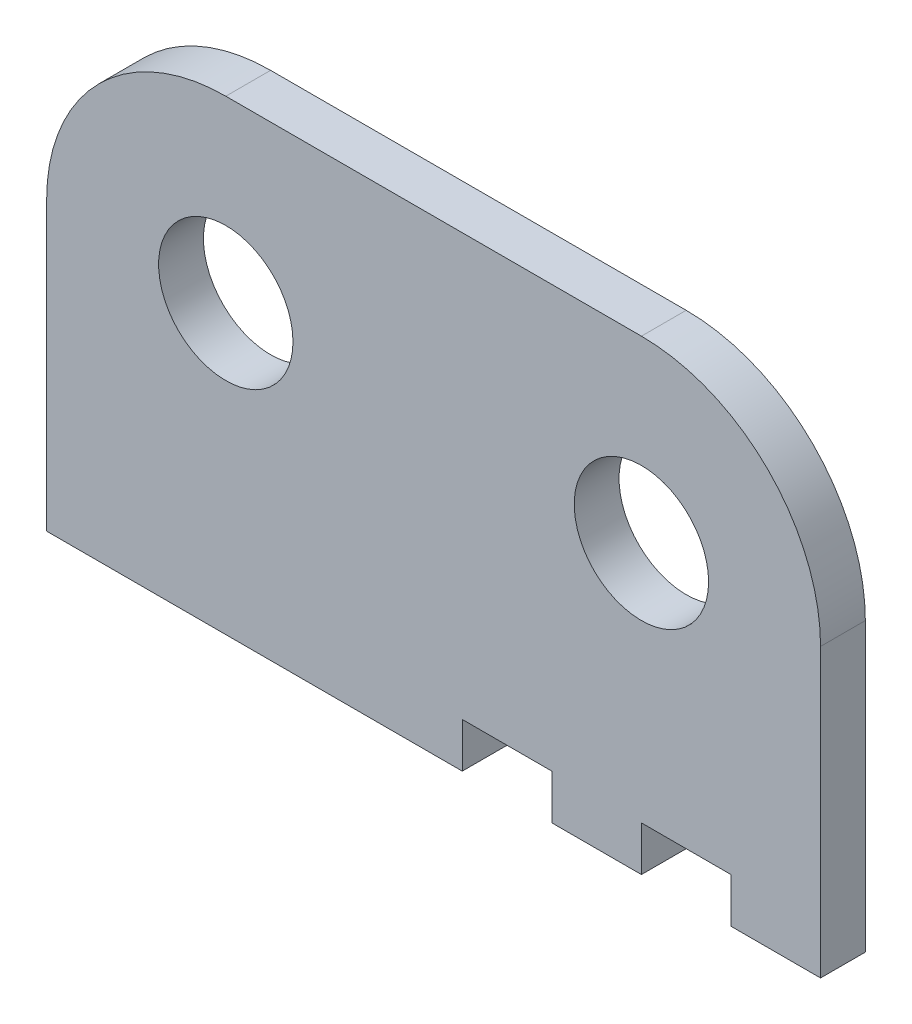
SolidWorks part; units mm, degrees
ref_plane "Front Plane" through (0, 0, 0) normal (0, 0, 1) x (1, 0, 0)
ref_plane "Top Plane" through (0, 0, 0) normal (0, 1, 0) x (1, 0, 0)
ref_plane "Right Plane" through (0, 0, 0) normal (1, 0, 0) x (0, 0, -1)
sketch "Sketch1" plane through (0, 0, 0) normal (0, 0, 1) x (1, 0, 0)
  line L0 (0, 0) -> (20.6877, 0) construction
  line L1 (20.6877, 0) -> (20.6877, 20.3568) construction
  line L2 (20.6877, 20.3568) -> (20.6877, 33.0568) construction
  line L3 (20.6877, 20.3568) -> (15.9252, 20.3568) construction
  line L4 (-8.7763, 20.3568) -> (-13.5388, 20.3568) construction
  line L8 (33.3877, 20.3568) -> (33.3877, 0)
  line L9 (-21.4763, 0) -> (33.3877, 0)
  line L10 (20.6877, 33.0568) -> (-8.7763, 33.0568)
  line L11 (-21.4763, 20.3568) -> (-21.4763, 0)
  line L12 (-4.0138, 20.3568) -> (-8.7763, 20.3568) construction
  line L13 (-21.4763, 20.3568) -> (-39.6056, 20.3568) construction
  line L14 (20.6877, 60.7428) -> (20.6877, 63.9178) construction
  circle A0 centre (20.6877, 20.3568) radius 4.7625
  circle A2 centre (-8.7763, 20.3568) radius 4.7625
  arc A6 (33.3877, 20.3568) -> (20.6877, 33.0568) centre (20.6877, 20.3568) ccw
  arc A7 (-8.7763, 33.0568) -> (-21.4763, 20.3568) centre (-8.7763, 20.3568) ccw
  point P24 (12.0754, -1.656)
  dimension "D2" = 9.525
  dimension "D5" = 9.525
  dimension "D12" = 25.4
  dimension "D13" = 25.4
  dimension "D1" = 20.3568
  dimension "D3" = 43.561
  dimension "D6" = 29.464
  dimension "D8" = 30.8293
extrude "Boss-Extrude1" add sketch "Sketch1" along normal blind 3.175
sketch "Sketch2" plane through (0, 0, 0) normal (0, -1, 0) x (1, 0, 0)
  line L0 (-21.4763, 0) -> (33.3877, 0) construction
  line L1 (20.6877, 0) -> (27.0377, 0)
  line L2 (20.6877, 0) -> (20.6877, 3.175)
  line L3 (20.6877, 3.175) -> (27.0377, 3.175)
  line L4 (27.0377, 0) -> (27.0377, 3.175)
  line L5 (-21.4763, 3.175) -> (33.3877, 3.175) construction
  line L6 (33.3877, 3.175) -> (33.3877, 0) construction
  line L8 (7.9877, 3.175) -> (14.3377, 3.175)
  line L9 (7.9877, 3.175) -> (7.9877, 0)
  line L10 (7.9877, 0) -> (14.3377, 0)
  line L11 (14.3377, 3.175) -> (14.3377, 0)
  point P14 (14.3377, 1.5875)
  dimension "D1" = 6.35
  dimension "D2" = 6.35
  dimension "D3" = 6.35
  dimension "D4" = 6.35
extrude "Cut-Extrude1" cut sketch "Sketch2" against normal blind 3.175
